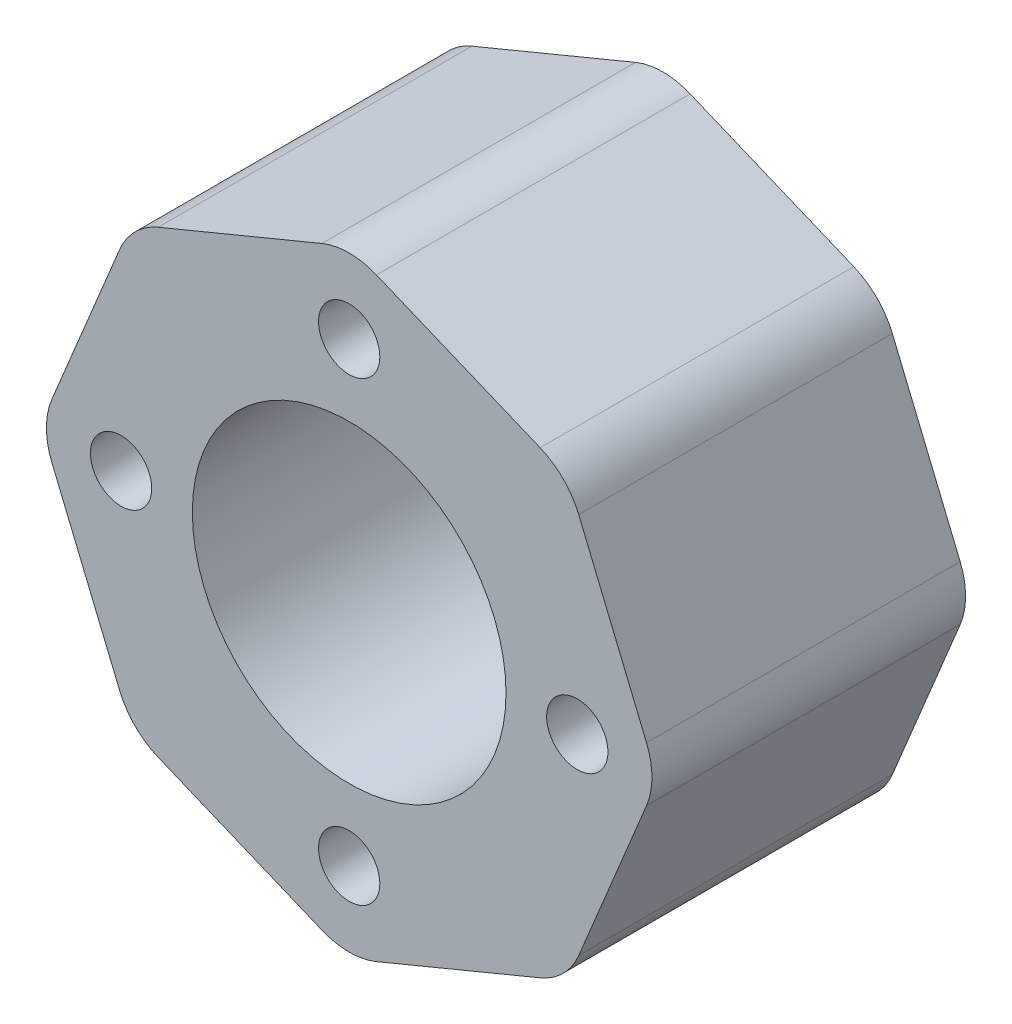
SolidWorks part; units mm, degrees
material "ABS"
ref_plane "Front Plane" through (0, 0, 0) normal (0, 0, 1) x (1, 0, 0)
ref_plane "Top Plane" through (0, 0, 0) normal (0, 1, 0) x (1, 0, 0)
ref_plane "Right Plane" through (0, 0, 0) normal (1, 0, 0) x (0, 0, -1)
sketch "Sketch1" plane through (0, 0, 0) normal (0, 0, 1) x (1, 0, 0)
  line L0 (0, -21.6478) -> (15.3073, -15.3073)
  line L1 (21.6478, 0) -> (15.3073, 15.3073)
  line L2 (15.3073, 15.3073) -> (0, 21.6478)
  line L3 (0, 21.6478) -> (-15.3073, 15.3073)
  line L4 (-15.3073, 15.3073) -> (-21.6478, 0)
  line L5 (-21.6478, 0) -> (-15.3073, -15.3073)
  line L6 (-15.3073, -15.3073) -> (0, -21.6478)
  line L7 (15.3073, -15.3073) -> (21.6478, 0)
  circle A0 centre (0, 0) radius 20 construction
  dimension "D1" = 40
extrude "Boss-Extrude1" add sketch "Sketch1" along normal blind 22
fillet "Fillet1" radius 5 8 edges at (15.3073, 15.3073, 11) (-15.3073, -15.3073, 11) (-21.6478, 0, 11) (-15.3073, 15.3073, 11) (0, 21.6478, 11) (21.6478, 0, 11) (15.3073, -15.3073, 11) (0, -21.6478, 11)
hole_wizard "M4 Clearance Hole1" positions "Sketch3" profile "Sketch4" hole size "M4" standard "ISO" end condition through all
sketch "Sketch3" plane through (0, 0, 22) normal (0, 0, 1) x (1, 0, 0)
  circle A0 centre (0, 0) radius 16 construction
  point P0 (0, 16)
  point P7 (16, 0)
  point P9 (0, -16)
  point P11 (-16, 0)
  dimension "D1" = 32
sketch "Sketch4" plane through (0, 16, 22) normal (1, 0, 0) x (0, -1, 0)
  line L0 (0, 0) -> (0, 22)
  line L1 (0, 22) -> (2.15, 22)
  line L2 (2.15, 22) -> (2.15, 0)
  line L5 (2.15, 0) -> (0, 0)
  line L11 (0, -6.35) -> (0, 107.95) construction
  dimension "Thru Hole Dia." = 4.3
  dimension "Thru Hole Depth" = 22
sketch "Sketch5" plane through (0, 0, 22) normal (0, 0, 1) x (1, 0, 0)
  circle A0 centre (0, 0) radius 11
  dimension "D1" = 22
extrude "Cut-Extrude1" cut sketch "Sketch5" against normal blind 22
